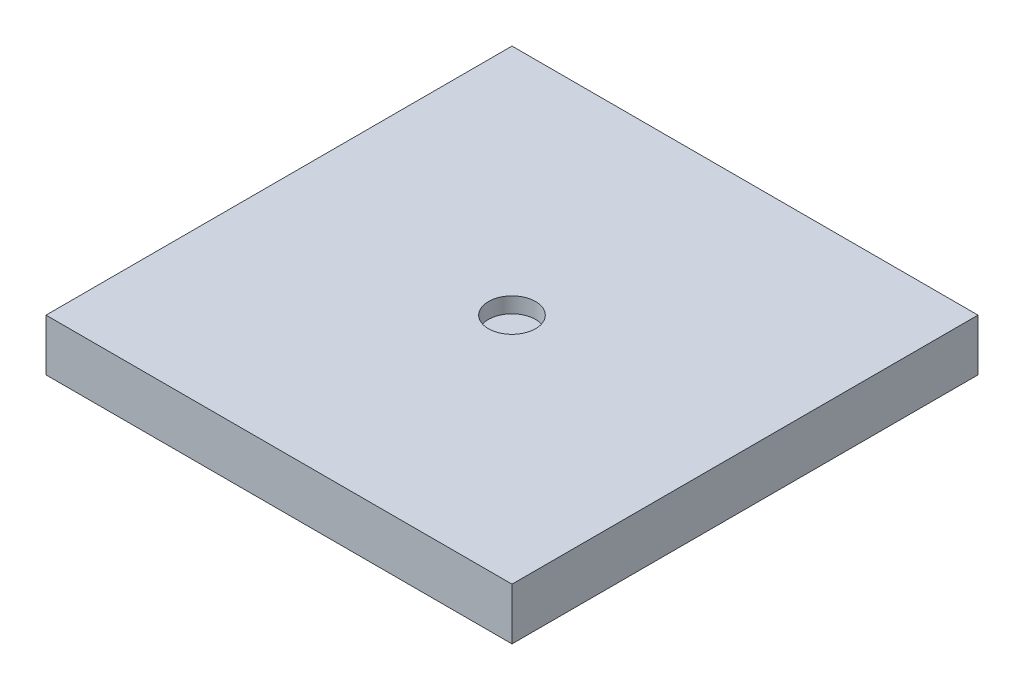
SolidWorks part; units mm, degrees
ref_plane "Front Plane" through (0, 0, 0) normal (0, 0, 1) x (1, 0, 0)
ref_plane "Top Plane" through (0, 0, 0) normal (0, 1, 0) x (1, 0, 0)
ref_plane "Right Plane" through (0, 0, 0) normal (1, 0, 0) x (0, 0, -1)
sketch "Sketch1" plane through (0, 0, 0) normal (0, 1, 0) x (1, 0, 0)
  line L1 (-11.43, -11.43) -> (11.43, -11.43)
  line L2 (-11.43, -11.43) -> (-11.43, 11.43)
  line L3 (-11.43, 11.43) -> (11.43, 11.43)
  line L4 (11.43, -11.43) -> (11.43, 11.43)
  line L5 (-11.43, -11.43) -> (11.43, 11.43) construction
  line L6 (-11.43, 11.43) -> (11.43, -11.43) construction
  point P0 (0, 0)
  dimension "D1" = 22.86
  dimension "D2" = 22.86
extrude "Boss-Extrude1" add sketch "Sketch1" along normal blind 2.54
sketch "Sketch2" plane through (0, 2.54, 0) normal (0, 1, 0) x (1, 0, 0)
  circle A0 centre (0, 0) radius 1.1565
extrude "Cut-Extrude1" cut sketch "Sketch2" against normal blind 0.762
